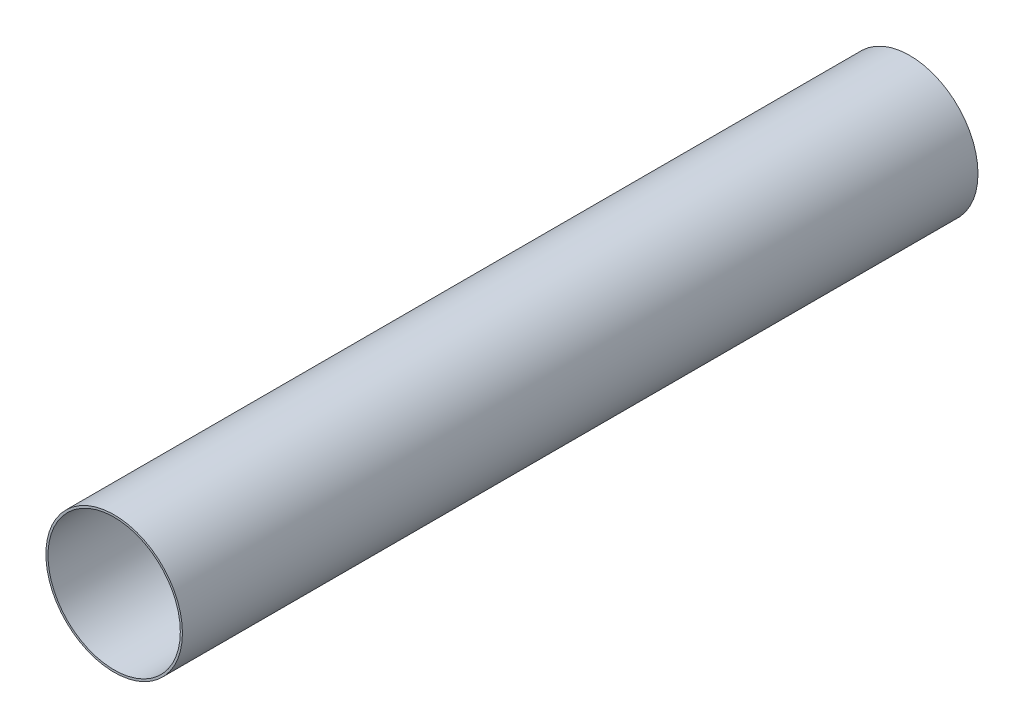
SolidWorks part; units mm, degrees
ref_plane "Front Plane" through (0, 0, 0) normal (0, 0, 1) x (1, 0, 0)
ref_plane "Top Plane" through (0, 0, 0) normal (0, 1, 0) x (1, 0, 0)
ref_plane "Right Plane" through (0, 0, 0) normal (1, 0, 0) x (0, 0, -1)
sketch "Sketch1" plane through (0, 0, 0) normal (0, 0, 1) x (1, 0, 0)
  circle A0 centre (0, 0) radius 65.405
  circle A1 centre (0, 0) radius 63.373
  dimension "D1" = 126.746
  dimension "D2" = 130.81
extrude "Boss-Extrude1" add sketch "Sketch1" along normal mid plane 762
equation "\"AIRFRAME_OD\"= 5.15in"
equation "\"AIRFRAME_ID\"= 4.99in"
equation "\"FLAT_T\"= 0.125in"
equation "\"NOSE_EXP_L\"= 27in"
equation "\"NOSE_SHOULDER_L\"= 5in"
equation "\"MAIN_L\"= 30in"
equation "\"RECO_COUP_L\"= 10in"
equation "\"RECO_SWITCH_L\"= 2in"
equation "\"DROGUE_L\"= 20in"
equation "\"ATS_FORE_COUP_L\"= 5.5in"
equation "\"ATS_AFT_COUP_L\"= 4.5in"
equation "\"LOWER_L\"= 30in"
equation "\"FIN_N\"= 4"
equation "\"CR_AFT_X\"= 0.5in"
equation "\"CR_FORE_X\"= 9.25in"
equation "\"D1@Sketch1\"=\"AIRFRAME_ID\""
equation "\"D2@Sketch1\"=\"AIRFRAME_OD\""
equation "\"D1@Boss-Extrude1\"=\"MAIN_L\""
equation "\"FIN_ROOT\"= 8in"
equation "\"FIN_X\"= 0.75in"
equation "\"MOTOR_OD\"= 3.091in"
equation "\"MOTOR_ID\"= 3.00in"
equation "\"COUPLER_OD\"= 4.998in"
equation "\"COUPLER_ID\"= 4.85in"
equation "\"RECO_ROD_X\"= 3.5in"
equation "\"ATS_ROD_X\"= 3.75in"
equation "\"MOTOR_L\"= 14in"
equation "\"MOTOR_LOWER_X\"= 2in"
